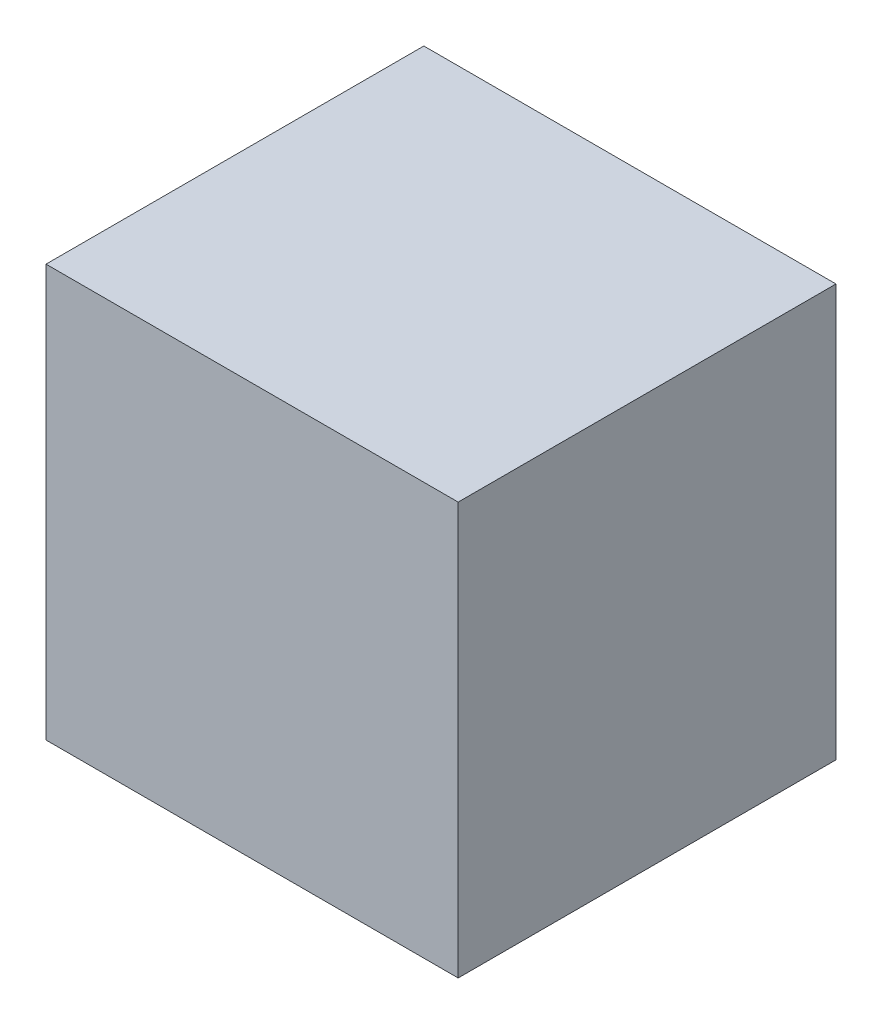
SolidWorks part; units mm, degrees
ref_plane "前视基准面" through (0, 0, 0) normal (0, 0, 1) x (1, 0, 0)
ref_plane "上视基准面" through (0, 0, 0) normal (0, 1, 0) x (1, 0, 0)
ref_plane "右视基准面" through (0, 0, 0) normal (1, 0, 0) x (0, 0, -1)
other "Configuration Table"
sketch "草图1" plane through (0, 0, 0) normal (0, 0, 1) x (1, 0, 0)
  line L1 (-600, -600) -> (600, -600)
  line L2 (-600, -600) -> (-600, 600)
  line L3 (-600, 600) -> (600, 600)
  line L4 (600, -600) -> (600, 600)
  line L5 (-600, -600) -> (600, 600) construction
  line L6 (-600, 600) -> (600, -600) construction
  point P0 (0, 0)
  dimension "D1" = 1200
extrude "凸台-拉伸1" add sketch "草图1" along normal blind 1100
